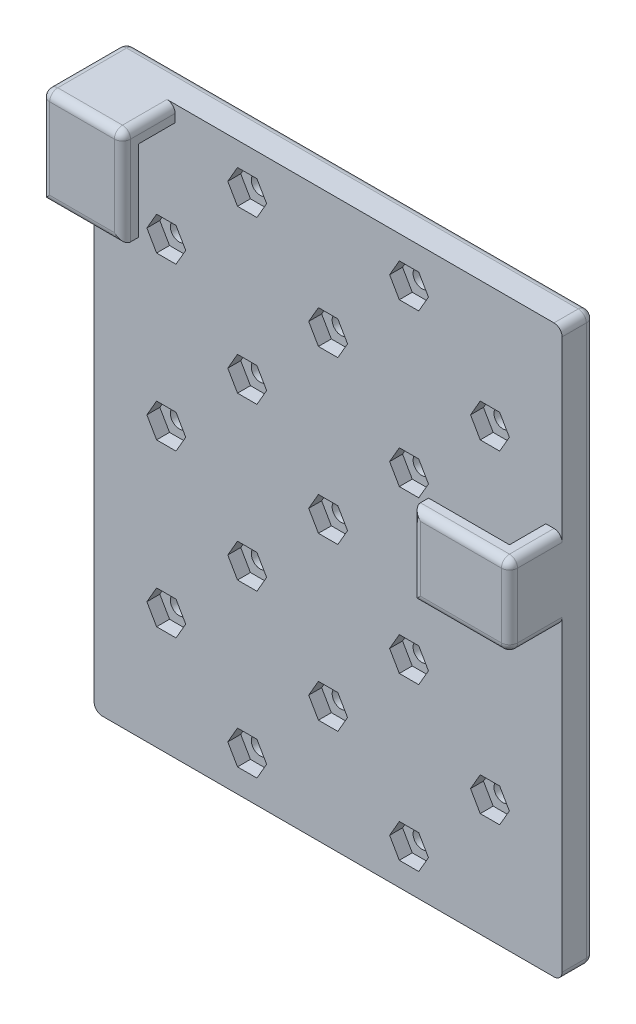
SolidWorks part; units mm, degrees
ref_plane "Plan de face" through (0, 0, 0) normal (0, 0, 1) x (1, 0, 0)
ref_plane "Plan de dessus" through (0, 0, 0) normal (0, 1, 0) x (1, 0, 0)
ref_plane "Plan de droite" through (0, 0, 0) normal (1, 0, 0) x (0, 0, -1)
sketch "Esquisse1" plane through (0, 0, 0) normal (0, 1, 0) x (1, 0, 0)
  line L0 (19.8322, -6.5) -> (31.8322, -6.5)
  line L1 (31.8322, -6.5) -> (31.8322, 2)
  line L3 (19.8322, -6.5) -> (19.8322, -4.5)
  line L4 (19.8322, -4.5) -> (29.8322, -4.5)
  line L5 (29.8322, -4.5) -> (29.8322, 0)
  line L6 (29.8322, 0) -> (-26, 0)
  line L7 (31.8322, 2) -> (-26, 2)
  line L8 (-26, 2) -> (-26, 0)
  dimension "D6" = 57.8322
  dimension "D7" = 26
  dimension "D1" = 10
  dimension "D2" = 2
  dimension "D3" = 2
  dimension "D4" = 2
  dimension "D5" = 8.5
  dimension "D8" = 4.5
extrude "Boss.-Extru.1" add sketch "Esquisse1" along normal blind 10
sketch "Esquisse4" plane through (-26, 0, 0) normal (-1, 0, 0) x (0, 0, 1)
  line L1 (-2, 10) -> (0, 10)
  line L2 (-2, 10) -> (-2, 32)
  line L3 (-2, 32) -> (6.5, 32)
  line L5 (0, 10) -> (0, 30)
  line L6 (0, 30) -> (4.5, 30)
  line L7 (4.5, 30) -> (4.5, 20)
  line L8 (4.5, 20) -> (6.5, 20)
  line L9 (6.5, 20) -> (6.5, 32)
  dimension "D1" = 22
  dimension "D2" = 4.5
  dimension "D3" = 10
  dimension "D4" = 2
  dimension "D5" = 2
extrude "Boss.-Extru.2" add sketch "Esquisse4" against normal blind 10
sketch "Esquisse5" plane through (0, 0, -2) normal (0, 0, -1) x (-1, 0, 0)
  line L1 (26, 32) -> (-31.8322, 32)
  line L2 (26, 32) -> (26, -38)
  line L3 (26, -38) -> (-31.8322, -38)
  line L4 (-31.8322, 32) -> (-31.8322, -38)
  line L5 (16, 32) -> (26, 32) construction
  line L6 (26, 32) -> (26, 0) construction
  line L7 (-31.8322, 10) -> (-31.8322, 0) construction
  dimension "D1" = 70
extrude "Boss.-Extru.3" add sketch "Esquisse5" along normal blind 2 and the other way blind 2
sketch "Esquisse6" plane through (0, 0, -4) normal (0, 0, -1) x (-1, 0, 0)
  line L1 (26, -38) -> (26, 32) construction
  line L2 (26, 32) -> (-31.8322, 32) construction
  circle A0 centre (7.0839, 27) radius 1.1
  circle A3 centre (17.0839, -3) radius 1.1
  circle A4 centre (7.0839, -33) radius 1.1
  circle A6 centre (-22.9161, 17) radius 1.1
  circle A7 centre (17.0839, 17) radius 1.1
  circle A8 centre (17.0839, -23) radius 1.1
  circle A9 centre (-12.9161, 27) radius 1.1
  circle A10 centre (-12.9161, -33) radius 1.1
  circle A11 centre (-22.9161, -3) radius 1.1
  circle A12 centre (-22.9161, -23) radius 1.1
  circle A13 centre (7.0839, -13) radius 1.1
  circle A14 centre (7.0839, 7) radius 1.1
  circle A15 centre (-2.9161, -23) radius 1.1
  circle A16 centre (-2.9161, -3) radius 1.1
  circle A17 centre (-2.9161, 17) radius 1.1
  circle A18 centre (-12.9161, 7) radius 1.1
  circle A19 centre (-12.9161, -13) radius 1.1
  point P10 (-2.9161, 32)
  point P11 (26, -3)
  dimension "D1" = 2.2
  dimension "D2" = 10
  dimension "D3" = 20
  dimension "D4" = 20
  dimension "D5" = 10
  dimension "D6" = 20
  dimension "D7" = 10
  dimension "D8" = 10
  dimension "D9" = 10
  dimension "D10" = 10
  dimension "D11" = 10
extrude "Enlèv. mat.-Extru.1" cut sketch "Esquisse6" against normal up to next
sketch "Esquisse7" plane through (0, 0, 0) normal (0, 0, 1) x (1, 0, 0)
  line L0 (-16, 32) -> (31.8322, 32) construction
  line L1 (11.7161, 24.9215) -> (14.1161, 24.9215)
  line L2 (14.1161, 24.9215) -> (15.3161, 27)
  line L3 (15.3161, 27) -> (14.1161, 29.0785)
  line L4 (14.1161, 29.0785) -> (11.7161, 29.0785)
  line L5 (11.7161, 29.0785) -> (10.5161, 27)
  line L6 (10.5161, 27) -> (11.7161, 24.9215)
  line L8 (-5.8839, 24.9215) -> (-4.6839, 27)
  line L9 (-4.6839, 27) -> (-5.8839, 29.0785)
  line L10 (-5.8839, 29.0785) -> (-8.2839, 29.0785)
  line L11 (-8.2839, 29.0785) -> (-9.4839, 27)
  line L12 (-9.4839, 27) -> (-8.2839, 24.9215)
  line L13 (-8.2839, 24.9215) -> (-5.8839, 24.9215)
  line L14 (-15.8839, 14.9215) -> (-14.6839, 17)
  line L15 (-14.6839, 17) -> (-15.8839, 19.0785)
  line L16 (-15.8839, 19.0785) -> (-18.2839, 19.0785)
  line L17 (-18.2839, 19.0785) -> (-19.4839, 17)
  line L18 (-19.4839, 17) -> (-18.2839, 14.9215)
  line L19 (-18.2839, 14.9215) -> (-15.8839, 14.9215)
  line L20 (24.1161, 14.9215) -> (25.3161, 17)
  line L21 (25.3161, 17) -> (24.1161, 19.0785)
  line L22 (24.1161, 19.0785) -> (21.7161, 19.0785)
  line L23 (21.7161, 19.0785) -> (20.5161, 17)
  line L24 (20.5161, 17) -> (21.7161, 14.9215)
  line L25 (21.7161, 14.9215) -> (24.1161, 14.9215)
  line L26 (24.1161, -5.0785) -> (25.3161, -3)
  line L27 (25.3161, -3) -> (24.1161, -0.9215)
  line L28 (24.1161, -0.9215) -> (21.7161, -0.9215)
  line L29 (21.7161, -0.9215) -> (20.5161, -3)
  line L30 (20.5161, -3) -> (21.7161, -5.0785)
  line L31 (21.7161, -5.0785) -> (24.1161, -5.0785)
  line L32 (-15.8839, -5.0785) -> (-14.6839, -3)
  line L33 (-14.6839, -3) -> (-15.8839, -0.9215)
  line L34 (-15.8839, -0.9215) -> (-18.2839, -0.9215)
  line L35 (-18.2839, -0.9215) -> (-19.4839, -3)
  line L36 (-19.4839, -3) -> (-18.2839, -5.0785)
  line L37 (-18.2839, -5.0785) -> (-15.8839, -5.0785)
  line L38 (24.1161, -25.0785) -> (25.3161, -23)
  line L39 (25.3161, -23) -> (24.1161, -20.9215)
  line L40 (24.1161, -20.9215) -> (21.7161, -20.9215)
  line L41 (21.7161, -20.9215) -> (20.5161, -23)
  line L42 (20.5161, -23) -> (21.7161, -25.0785)
  line L43 (21.7161, -25.0785) -> (24.1161, -25.0785)
  line L44 (14.1161, -35.0785) -> (15.3161, -33)
  line L45 (15.3161, -33) -> (14.1161, -30.9215)
  line L46 (14.1161, -30.9215) -> (11.7161, -30.9215)
  line L47 (11.7161, -30.9215) -> (10.5161, -33)
  line L48 (10.5161, -33) -> (11.7161, -35.0785)
  line L49 (11.7161, -35.0785) -> (14.1161, -35.0785)
  line L50 (-5.8839, -35.0785) -> (-4.6839, -33)
  line L51 (-4.6839, -33) -> (-5.8839, -30.9215)
  line L52 (-5.8839, -30.9215) -> (-8.2839, -30.9215)
  line L53 (-8.2839, -30.9215) -> (-9.4839, -33)
  line L54 (-9.4839, -33) -> (-8.2839, -35.0785)
  line L55 (-8.2839, -35.0785) -> (-5.8839, -35.0785)
  line L56 (-15.8839, -25.0785) -> (-14.6839, -23)
  line L57 (-14.6839, -23) -> (-15.8839, -20.9215)
  line L58 (-15.8839, -20.9215) -> (-18.2839, -20.9215)
  line L59 (-18.2839, -20.9215) -> (-19.4839, -23)
  line L60 (-19.4839, -23) -> (-18.2839, -25.0785)
  line L61 (-18.2839, -25.0785) -> (-15.8839, -25.0785)
  line L62 (4.1161, 14.9215) -> (5.3161, 17)
  line L63 (5.3161, 17) -> (4.1161, 19.0785)
  line L64 (4.1161, 19.0785) -> (1.7161, 19.0785)
  line L65 (1.7161, 19.0785) -> (0.5161, 17)
  line L66 (0.5161, 17) -> (1.7161, 14.9215)
  line L67 (1.7161, 14.9215) -> (4.1161, 14.9215)
  line L68 (14.1161, 4.9215) -> (15.3161, 7)
  line L69 (15.3161, 7) -> (14.1161, 9.0785)
  line L70 (14.1161, 9.0785) -> (11.7161, 9.0785)
  line L71 (11.7161, 9.0785) -> (10.5161, 7)
  line L72 (10.5161, 7) -> (11.7161, 4.9215)
  line L73 (11.7161, 4.9215) -> (14.1161, 4.9215)
  line L74 (-5.8839, 4.9215) -> (-4.6839, 7)
  line L75 (-4.6839, 7) -> (-5.8839, 9.0785)
  line L76 (-5.8839, 9.0785) -> (-8.2839, 9.0785)
  line L77 (-8.2839, 9.0785) -> (-9.4839, 7)
  line L78 (-9.4839, 7) -> (-8.2839, 4.9215)
  line L79 (-8.2839, 4.9215) -> (-5.8839, 4.9215)
  line L80 (4.1161, -5.0785) -> (5.3161, -3)
  line L81 (5.3161, -3) -> (4.1161, -0.9215)
  line L82 (4.1161, -0.9215) -> (1.7161, -0.9215)
  line L83 (1.7161, -0.9215) -> (0.5161, -3)
  line L84 (0.5161, -3) -> (1.7161, -5.0785)
  line L85 (1.7161, -5.0785) -> (4.1161, -5.0785)
  line L86 (-5.8839, -15.0785) -> (-4.6839, -13)
  line L87 (-4.6839, -13) -> (-5.8839, -10.9215)
  line L88 (-5.8839, -10.9215) -> (-8.2839, -10.9215)
  line L89 (-8.2839, -10.9215) -> (-9.4839, -13)
  line L90 (-9.4839, -13) -> (-8.2839, -15.0785)
  line L91 (-8.2839, -15.0785) -> (-5.8839, -15.0785)
  line L92 (4.1161, -25.0785) -> (5.3161, -23)
  line L93 (5.3161, -23) -> (4.1161, -20.9215)
  line L94 (4.1161, -20.9215) -> (1.7161, -20.9215)
  line L95 (1.7161, -20.9215) -> (0.5161, -23)
  line L96 (0.5161, -23) -> (1.7161, -25.0785)
  line L97 (1.7161, -25.0785) -> (4.1161, -25.0785)
  line L98 (14.1161, -15.0785) -> (15.3161, -13)
  line L99 (15.3161, -13) -> (14.1161, -10.9215)
  line L100 (14.1161, -10.9215) -> (11.7161, -10.9215)
  line L101 (11.7161, -10.9215) -> (10.5161, -13)
  line L102 (10.5161, -13) -> (11.7161, -15.0785)
  line L103 (11.7161, -15.0785) -> (14.1161, -15.0785)
  circle A0 centre (12.9161, 27) radius 2.0785 construction
  circle A1 centre (-7.0839, 27) radius 2.0785 construction
  circle A2 centre (-17.0839, 17) radius 2.0785 construction
  circle A3 centre (22.9161, 17) radius 2.0785 construction
  circle A4 centre (22.9161, -3) radius 2.0785 construction
  circle A5 centre (-17.0839, -3) radius 2.0785 construction
  circle A6 centre (22.9161, -23) radius 2.0785 construction
  circle A7 centre (12.9161, -33) radius 2.0785 construction
  circle A8 centre (-7.0839, -33) radius 2.0785 construction
  circle A9 centre (-17.0839, -23) radius 2.0785 construction
  circle A10 centre (2.9161, 17) radius 2.0785 construction
  circle A11 centre (12.9161, 7) radius 2.0785 construction
  circle A12 centre (-7.0839, 7) radius 2.0785 construction
  circle A13 centre (2.9161, -3) radius 2.0785 construction
  circle A14 centre (-7.0839, -13) radius 2.0785 construction
  circle A15 centre (2.9161, -23) radius 2.0785 construction
  circle A16 centre (12.9161, -13) radius 2.0785 construction
  dimension "D1" = 2.4
extrude "Enlèv. mat.-Extru.2" cut sketch "Esquisse7" against normal blind 1.6
fillet "Congé2" radius 1 19 edges at (-26, 32, 1.25) (2.9161, -38, -4) (-26, -38, -2) (-26, -3, -4) (31.8322, -38, -2) (31.8322, 32, -2) (31.8322, -3, -4) (2.9161, 32, -4) (25.8322, 10, 6.5) (19.8322, 5, 6.5) (25.8322, 0, 6.5) (-16, 32, 3.25) (-21, 20, 6.5) (-16, 26, 6.5) (-26, 26, 6.5) (-21, 32, 6.5) (31.8322, 5, 6.5) (31.8322, 0, 3.25) (31.8322, 10, 3.25)
